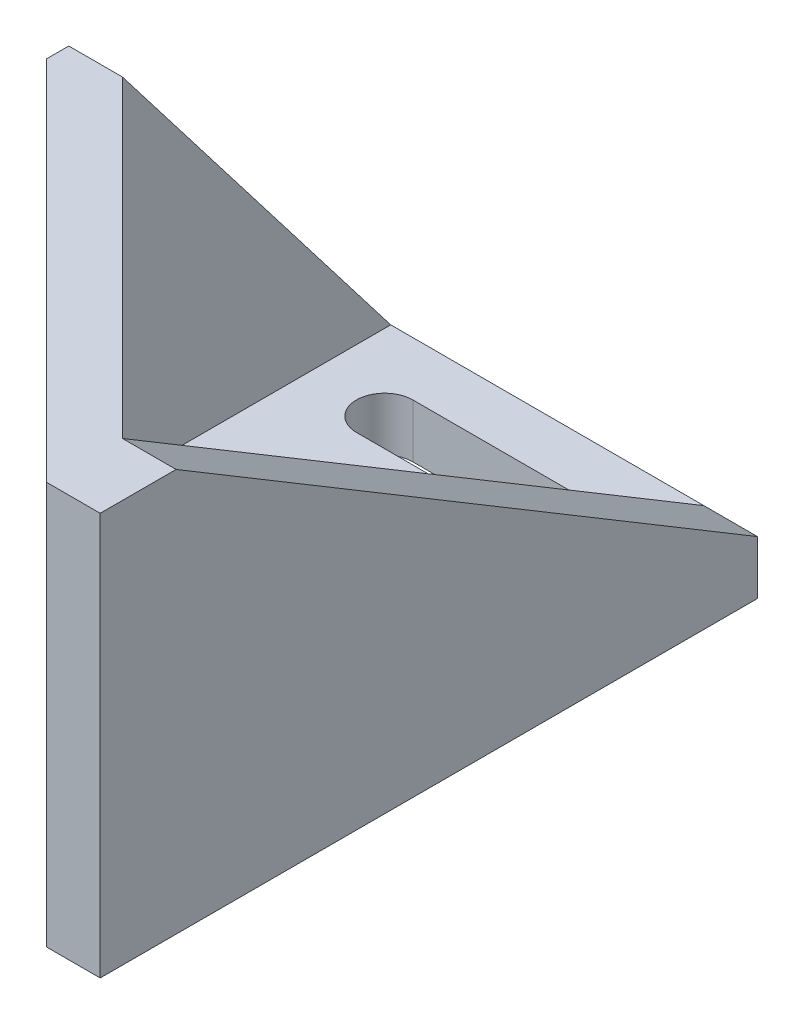
SolidWorks part; units mm, degrees
ref_plane "Alzado" through (0, 0, 0) normal (0, 0, 1) x (1, 0, 0)
ref_plane "Planta" through (0, 0, 0) normal (0, 1, 0) x (1, 0, 0)
ref_plane "Vista lateral" through (0, 0, 0) normal (1, 0, 0) x (0, 0, -1)
sketch "Croquis1" plane through (0, 0, 0) normal (0, 1, 0) x (1, 0, 0)
  line L0 (-11.6673, 1.6673) -> (11.6673, -21.6673)
  line L1 (-11.6673, -21.6673) -> (11.6673, -21.6673) construction
  line L2 (-11.6673, -21.6673) -> (-11.6673, 21.6673) construction
  line L3 (-11.6673, 21.6673) -> (11.6673, 21.6673)
  line L4 (11.6673, -21.6673) -> (11.6673, 21.6673)
  line L5 (-11.6673, -21.6673) -> (11.6673, 21.6673) construction
  line L6 (-11.6673, 21.6673) -> (11.6673, -21.6673) construction
  line L7 (-11.6673, 21.6673) -> (-11.6673, 1.6673)
  point P0 (0, 0)
  dimension "D1" = 45
  dimension "D2" = 20
  dimension "D3" = 33
extrude "Saliente-Extruir1" add sketch "Croquis1" along normal blind 4
sketch "Croquis3" plane through (0, 0, 0) normal (0, -1, 0) x (1, 0, 0)
  line L0 (-11.6673, -1.6673) -> (-11.6673, 3.9896)
  line L1 (-11.6673, 3.9896) -> (11.6673, 27.3241)
  line L2 (11.6673, 21.6673) -> (11.6673, 27.3241)
  line L4 (11.6673, 21.6673) -> (11.6673, -21.6673) construction
  line L5 (11.6673, 21.6673) -> (-11.6673, -1.6673)
  line L6 (11.6673, 21.6673) -> (11.6673, -21.6673) construction
  line L7 (-11.6673, -1.6673) -> (11.6673, 21.6673) construction
  dimension "D1" = 4
extrude "Saliente-Extruir2" add sketch "Croquis3" against normal blind 30
sketch "Croquis7" plane through (11.6673, 0, 0) normal (1, 0, 0) x (0, 0, -1)
  line L0 (-21.6673, 30) -> (21.6673, 4)
  line L1 (-21.6673, 30) -> (-27.3241, 30) construction
  line L2 (-27.3241, 30) -> (-27.3241, 0) construction
  line L3 (-27.3241, 0) -> (21.6673, 0) construction
  line L4 (21.6673, 4) -> (21.6673, 0) construction
  line L5 (-21.6673, 30) -> (-27.3241, 30)
  line L6 (-27.3241, 30) -> (-27.3241, 0)
  line L7 (-27.3241, 0) -> (21.6673, 0)
  line L8 (21.6673, 4) -> (21.6673, 0)
extrude "Saliente-Extruir5" add sketch "Croquis7" along normal blind 4
sketch "Croquis10" plane through (-11.6673, 0, 0) normal (-1, 0, 0) x (0, 0, 1)
  line L0 (-1.6673, 30) -> (-21.6673, 4)
  line L1 (-21.6673, 4) -> (-21.6673, 0) construction
  line L2 (-21.6673, 0) -> (3.9896, 0) construction
  line L3 (3.9896, 30) -> (3.9896, 0) construction
  line L4 (3.9896, 30) -> (-1.6673, 30) construction
  line L5 (-21.6673, 4) -> (-21.6673, 0)
  line L6 (-21.6673, 0) -> (3.9896, 0)
  line L7 (3.9896, 30) -> (3.9896, 0)
  line L8 (3.9896, 30) -> (-1.6673, 30)
extrude "Saliente-Extruir7" add sketch "Croquis10" along normal blind 4
sketch "Croquis11" plane through (0, 30, 0) normal (0, 1, 0) x (1, 0, 0)
  line L0 (-11.6673, -3.9896) -> (-15.6673, 0.0104)
  line L1 (-11.6673, 1.6673) -> (11.6673, -21.6673) construction
  line L2 (-15.6673, -3.9896) -> (-15.6673, 1.6673) construction
  line L3 (-15.6673, 0.0104) -> (-15.6673, -3.9896)
  line L4 (-15.6673, -3.9896) -> (-11.6673, -3.9896)
extrude "Cortar-Extruir2" cut sketch "Croquis11" against normal through all
sketch "Croquis12" plane through (-7.8284, 0, 7.8284) normal (-0.7071, 0, 0.7071) x (0.7071, 0, 0.7071)
  line L4 (-0.9289, 10.875) -> (-0.9289, 19.875)
  line L5 (20.0711, 10.875) -> (20.0711, 19.875)
  line L6 (15.0711, 19.875) -> (15.0711, 10.875)
  line L7 (-5.9289, 19.875) -> (-5.9289, 10.875)
  line L8 (-9.4289, 30) -> (-9.4289, 4) construction
  line L9 (-15.7237, 4) -> (32.2089, 4) construction
  line L12 (-3.4289, 19.875) -> (-3.4289, 10.875) construction
  line L13 (27.5711, 0) -> (-11.0858, 0) construction
  line L14 (8.2426, 30) -> (8.2426, 4) construction
  line L15 (27.5711, 30) -> (-11.0858, 30) construction
  line L16 (-3.4289, 15.375) -> (8.2426, 15.375) construction
  arc A4 (-0.9289, 19.875) -> (-5.9289, 19.875) centre (-3.4289, 19.875) ccw
  arc A5 (20.0711, 19.875) -> (15.0711, 19.875) centre (17.5711, 19.875) ccw
  arc A6 (-5.9289, 10.875) -> (-0.9289, 10.875) centre (-3.4289, 10.875) ccw
  arc A7 (15.0711, 10.875) -> (20.0711, 10.875) centre (17.5711, 10.875) ccw
  dimension "D2" = 2.5
  dimension "D1" = 21
  dimension "D3" = 9
  dimension "D4" = 6
  dimension "D5" = 4
sketch "Croquis13" plane through (-7.8284, 0, 7.8284) normal (-0.7071, 0, 0.7071) x (0.7071, 0, 0.7071)
  line L0 (-3.4289, 19.875) -> (-3.4289, 10.875) construction
  line L2 (17.5711, 10.875) -> (17.5711, 19.875) construction
  circle A0 centre (-3.4289, 15.375) radius 2.05
  circle A1 centre (17.5711, 15.375) radius 2.05
  dimension "D1" = 4.1
extrude "Cortar-Extruir3" cut sketch "Croquis13" against normal up to surface (4 mm away) up to face at (0, 17, 10)
sketch "Croquis14" plane through (0, 4, 0) normal (0, 1, 0) x (1, 0, 0)
  line L0 (-6, 15.5443) -> (6, 15.5443) construction
  line L1 (-6, 17.6443) -> (6, 17.6443)
  line L2 (-6, 13.4443) -> (6, 13.4443)
  line L3 (-6, 5.5443) -> (6, 5.5443) construction
  line L4 (-6, 7.6443) -> (6, 7.6443)
  line L5 (-6, 3.4443) -> (6, 3.4443)
  line L6 (0, 21.6673) -> (0, 15.5443) construction
  line L7 (11.6673, 21.6673) -> (-11.6673, 21.6673) construction
  arc A0 (-6, 17.6443) -> (-6, 13.4443) centre (-6, 15.5443) ccw
  arc A1 (6, 13.4443) -> (6, 17.6443) centre (6, 15.5443) ccw
  arc A2 (-6, 7.6443) -> (-6, 3.4443) centre (-6, 5.5443) ccw
  arc A3 (6, 3.4443) -> (6, 7.6443) centre (6, 5.5443) ccw
  point P2 (0, 15.5443)
  point P7 (0, 5.5443)
  dimension "D1" = 2.1
  dimension "D2" = 10
  dimension "D3" = 12
extrude "Cortar-Extruir4" cut sketch "Croquis14" against normal through all
sketch "Croquis15" plane through (-5, 0, 5) normal (0.7071, 0, -0.7071) x (-0.7071, 0, -0.7071)
  line L1 (-13.5874, 15.375) -> (-15.5792, 18.825)
  line L2 (-15.5792, 18.825) -> (-19.5629, 18.825)
  line L3 (-19.5629, 18.825) -> (-21.5548, 15.375)
  line L4 (-21.5548, 15.375) -> (-19.5629, 11.925)
  line L5 (-19.5629, 11.925) -> (-15.5792, 11.925)
  line L6 (-15.5792, 11.925) -> (-13.5874, 15.375)
  line L7 (-0.5548, 15.375) -> (1.4371, 11.925)
  line L8 (1.4371, 11.925) -> (5.4208, 11.925)
  line L9 (5.4208, 11.925) -> (7.4126, 15.375)
  line L10 (7.4126, 15.375) -> (5.4208, 18.825)
  line L11 (5.4208, 18.825) -> (1.4371, 18.825)
  line L12 (1.4371, 18.825) -> (-0.5548, 15.375)
  circle A0 centre (-17.5711, 15.375) radius 3.45 construction
  circle A1 centre (3.4289, 15.375) radius 3.45 construction
  dimension "D1" = 6.9
extrude "Cortar-Extruir5" cut sketch "Croquis15" against normal blind 2
